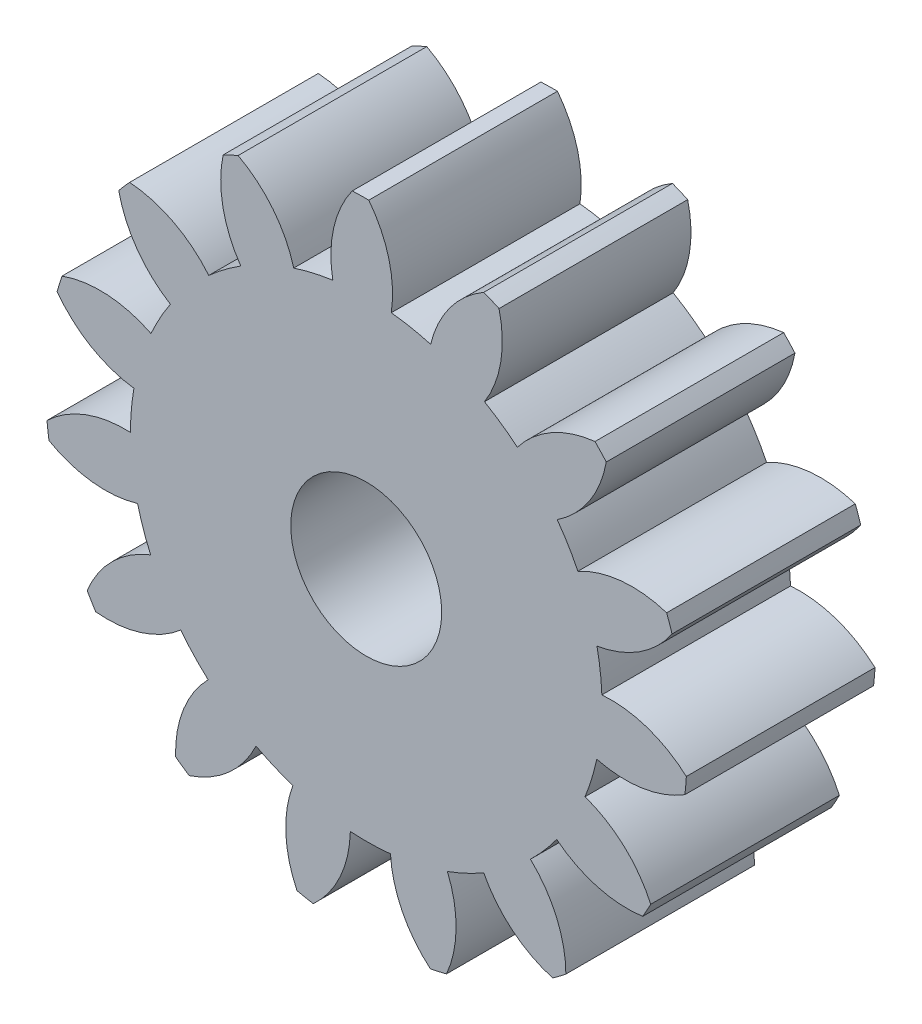
SolidWorks part; units mm, degrees
ref_plane "Front Plane" through (0, 0, 0) normal (0, 0, 1) x (1, 0, 0)
ref_plane "Top Plane" through (0, 0, 0) normal (0, 1, 0) x (1, 0, 0)
ref_plane "Right Plane" through (0, 0, 0) normal (1, 0, 0) x (0, 0, -1)
sketch "Model" plane through (0, 0, 0) normal (0, 0, 1) x (1, 0, 0)
  arc A0 (455.2138, 475.7371) -> (455.911, 476.5397) centre (450.862, 480.2216) ccw
  arc A1 (456.1531, 473.5693) -> (455.2138, 475.7371) centre (453.1531, 473.5568) ccw
  arc A2 (455.8028, 473.3051) -> (456.1531, 473.5693) centre (450.862, 480.2216) ccw
  arc A3 (453.9769, 474.8043) -> (455.8028, 473.3051) centre (456.6398, 476.186) ccw
  arc A4 (453.0135, 474.3547) -> (453.9769, 474.8043) centre (450.862, 480.2216) ccw
  arc A5 (452.9899, 471.9923) -> (453.0135, 474.3547) centre (450.2442, 473.2011) ccw
  arc A6 (452.5624, 471.8935) -> (452.9899, 471.9923) centre (450.862, 480.2216) ccw
  arc A7 (451.5042, 474.0057) -> (452.5624, 471.8935) centre (454.4989, 474.1848) ccw
  arc A8 (450.4412, 473.9868) -> (451.5042, 474.0057) centre (450.862, 480.2216) ccw
  arc A9 (449.4588, 471.8383) -> (450.4412, 473.9868) centre (447.4421, 474.0593) ccw
  arc A10 (449.0281, 471.9218) -> (449.4588, 471.8383) centre (450.862, 480.2216) ccw
  arc A11 (448.9204, 474.2819) -> (449.0281, 471.9218) centre (451.729, 473.2275) ccw
  arc A12 (447.9417, 474.697) -> (448.9204, 474.2819) centre (450.862, 480.2216) ccw
  arc A13 (446.1703, 473.1338) -> (447.9417, 474.697) centre (445.2313, 475.9831) ccw
  arc A14 (445.8108, 473.3853) -> (446.1703, 473.1338) centre (450.862, 480.2216) ccw
  arc A15 (446.6724, 475.5851) -> (445.8108, 473.3853) centre (448.8093, 473.4795) ccw
  arc A16 (445.9471, 476.3624) -> (446.6724, 475.5851) centre (450.862, 480.2216) ccw
  arc A17 (443.693, 475.6549) -> (445.9471, 476.3624) centre (443.9941, 478.6397) ccw
  arc A18 (443.4669, 476.0309) -> (443.693, 475.6549) centre (450.862, 480.2216) ccw
  arc A19 (445.1488, 477.69) -> (443.4669, 476.0309) centre (446.2445, 474.8973) ccw
  arc A20 (444.8023, 478.6951) -> (445.1488, 477.69) centre (450.862, 480.2216) ccw
  arc A21 (442.4553, 478.9656) -> (444.8023, 478.6951) centre (443.9444, 481.5699) ccw
  arc A22 (442.4017, 479.401) -> (442.4553, 478.9656) centre (450.862, 480.2216) ccw
  arc A23 (444.613, 480.2327) -> (442.4017, 479.401) centre (444.4781, 477.2357) ccw
  arc A24 (444.7053, 481.2918) -> (444.613, 480.2327) centre (450.862, 480.2216) ccw
  arc A25 (442.6712, 482.4935) -> (444.7053, 481.2918) centre (445.0909, 484.2669) ccw
  arc A26 (442.7993, 482.9131) -> (442.6712, 482.4935) centre (450.862, 480.2216) ccw
  arc A27 (445.1577, 482.7734) -> (442.7993, 482.9131) centre (443.8155, 480.0904) ccw
  arc A28 (445.6728, 483.7034) -> (445.1577, 482.7734) centre (450.862, 480.2216) ccw
  arc A29 (444.3034, 485.6285) -> (445.6728, 483.7034) centre (447.2352, 486.2645) ccw
  arc A30 (444.5911, 485.9598) -> (444.3034, 485.6285) centre (450.862, 480.2216) ccw
  arc A31 (446.6888, 484.8729) -> (444.5911, 485.9598) centre (444.3713, 482.9678) ccw
  arc A32 (447.5376, 485.513) -> (446.6888, 484.8729) centre (450.862, 480.2216) ccw
  arc A33 (447.0696, 487.8287) -> (447.5376, 485.513) centre (450.0066, 487.2172) ccw
  arc A34 (447.4672, 488.0143) -> (447.0696, 487.8287) centre (450.862, 480.2216) ccw
  arc A35 (448.9414, 486.1682) -> (447.4672, 488.0143) centre (446.0495, 485.3704) ccw
  arc A36 (449.9773, 486.4077) -> (448.9414, 486.1682) centre (450.862, 480.2216) ccw
  arc A37 (450.4915, 488.7136) -> (449.9773, 486.4077) centre (452.9259, 486.9604) ccw
  arc A38 (450.9302, 488.7214) -> (450.4915, 488.7136) centre (450.862, 480.2216) ccw
  arc A39 (451.5261, 486.4353) -> (450.9302, 488.7214) centre (448.5597, 486.8827) ccw
  arc A40 (452.5698, 486.2327) -> (451.5261, 486.4353) centre (450.862, 480.2216) ccw
  arc A41 (453.9775, 488.1301) -> (452.5698, 486.2327) centre (455.4884, 485.5383) ccw
  arc A42 (454.3815, 487.9588) -> (453.9775, 488.1301) centre (450.862, 480.2216) ccw
  arc A43 (453.996, 485.6279) -> (454.3815, 487.9588) centre (451.468, 487.2432) ccw
  arc A44 (454.8671, 485.0184) -> (453.996, 485.6279) centre (450.862, 480.2216) ccw
  arc A45 (456.9248, 486.1792) -> (454.8671, 485.0184) centre (457.2509, 483.1969) ccw
  arc A46 (457.2242, 485.8584) -> (456.9248, 486.1792) centre (450.862, 480.2216) ccw
  arc A47 (455.924, 483.8858) -> (457.2242, 485.8584) centre (454.2716, 486.3897) ccw
  arc A48 (456.4719, 482.9747) -> (455.924, 483.8858) centre (450.862, 480.2216) ccw
  arc A49 (458.8238, 483.1981) -> (456.4719, 482.9747) centre (457.9087, 480.3411) ccw
  arc A50 (458.9668, 482.7833) -> (458.8238, 483.1981) centre (450.862, 480.2216) ccw
  arc A51 (456.9767, 481.5101) -> (458.9668, 482.7833) centre (456.4856, 484.4696) ccw
  arc A52 (457.1066, 480.4549) -> (456.9767, 481.5101) centre (450.862, 480.2216) ccw
  arc A53 (459.3461, 479.7024) -> (457.1066, 480.4549) centre (457.348, 477.4646) ccw
  arc A54 (459.308, 479.2653) -> (459.3461, 479.7024) centre (450.862, 480.2216) ccw
  arc A55 (456.9721, 478.9116) -> (459.308, 479.2653) centre (457.7272, 481.815) ccw
  arc A56 (456.6616, 477.8948) -> (456.9721, 478.9116) centre (450.862, 480.2216) ccw
  arc A57 (458.4014, 476.2965) -> (456.6616, 477.8948) centre (455.6659, 475.0649) ccw
  arc A58 (458.1888, 475.9127) -> (458.4014, 476.2965) centre (450.862, 480.2216) ccw
  arc A59 (455.911, 476.5397) -> (458.1888, 475.9127) centre (457.7818, 478.885) ccw
  circle A60 centre (450.862, 480.2216) radius 2
extrude "Boss-Extrude1" add sketch "Model" along normal blind 5
